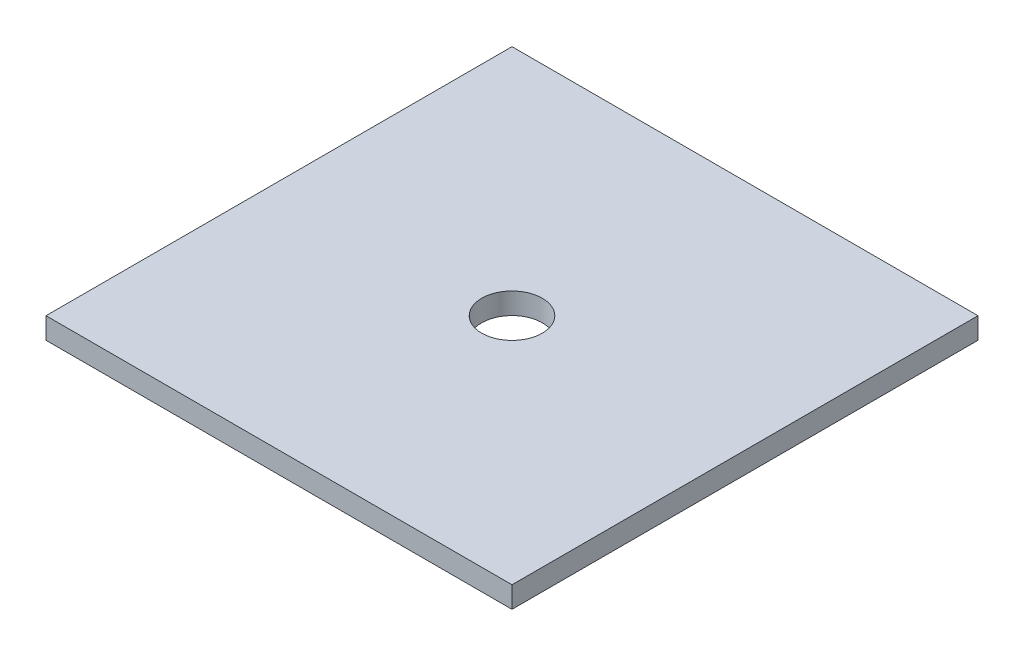
SolidWorks part; units mm, degrees
ref_plane "Alzado" through (0, 0, 0) normal (0, 0, 1) x (1, 0, 0)
ref_plane "Planta" through (0, 0, 0) normal (0, 1, 0) x (1, 0, 0)
ref_plane "Vista lateral" through (0, 0, 0) normal (1, 0, 0) x (0, 0, -1)
sketch "Croquis1" plane through (0, 0, 0) normal (0, 1, 0) x (1, 0, 0)
  line L1 (175, 175) -> (-175, 175)
  line L2 (175, 175) -> (175, -175)
  line L3 (175, -175) -> (-175, -175)
  line L4 (-175, 175) -> (-175, -175)
  line L5 (175, 175) -> (-175, -175) construction
  line L6 (175, -175) -> (-175, 175) construction
  circle A0 centre (0, 0) radius 22.75
  point P0 (0, 0)
  dimension "D3" = 45.5
  dimension "D1" = 350
  dimension "D2" = 350
extrude "Saliente-Extruir1" add sketch "Croquis1" along normal blind 16
